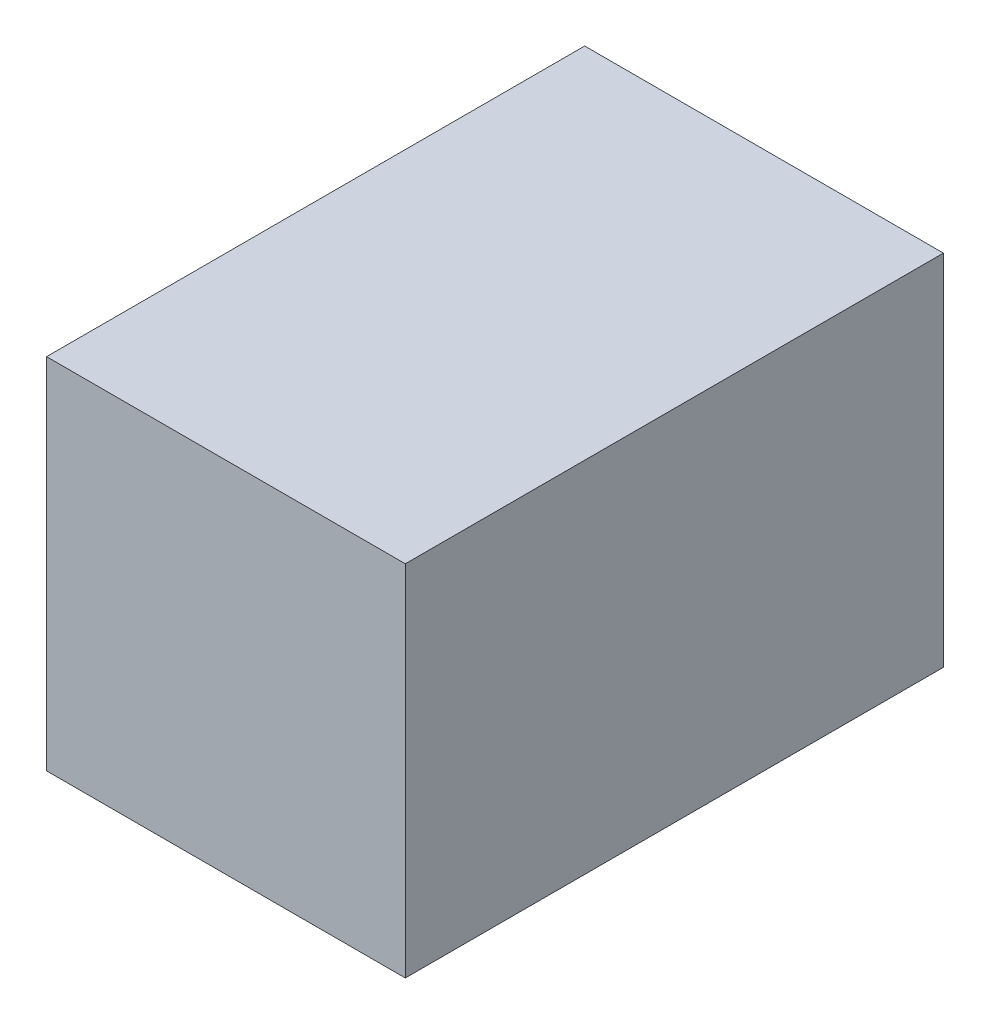
SolidWorks part; units mm, degrees
material "ABS"
ref_plane "Front Plane" through (0, 0, 0) normal (0, 0, 1) x (1, 0, 0)
ref_plane "Top Plane" through (0, 0, 0) normal (0, 1, 0) x (1, 0, 0)
ref_plane "Right Plane" through (0, 0, 0) normal (1, 0, 0) x (0, 0, -1)
sketch "Sketch1" plane through (0, 0, 0) normal (0, 0, 1) x (1, 0, 0)
  line L1 (-25, -25) -> (25, -25)
  line L2 (-25, -25) -> (-25, 25)
  line L3 (-25, 25) -> (25, 25)
  line L4 (25, -25) -> (25, 25)
  line L5 (-25, -25) -> (25, 25) construction
  line L6 (-25, 25) -> (25, -25) construction
  point P0 (0, 0)
  dimension "D1" = 50
extrude "Boss-Extrude1" add sketch "Sketch1" along normal mid plane 75
